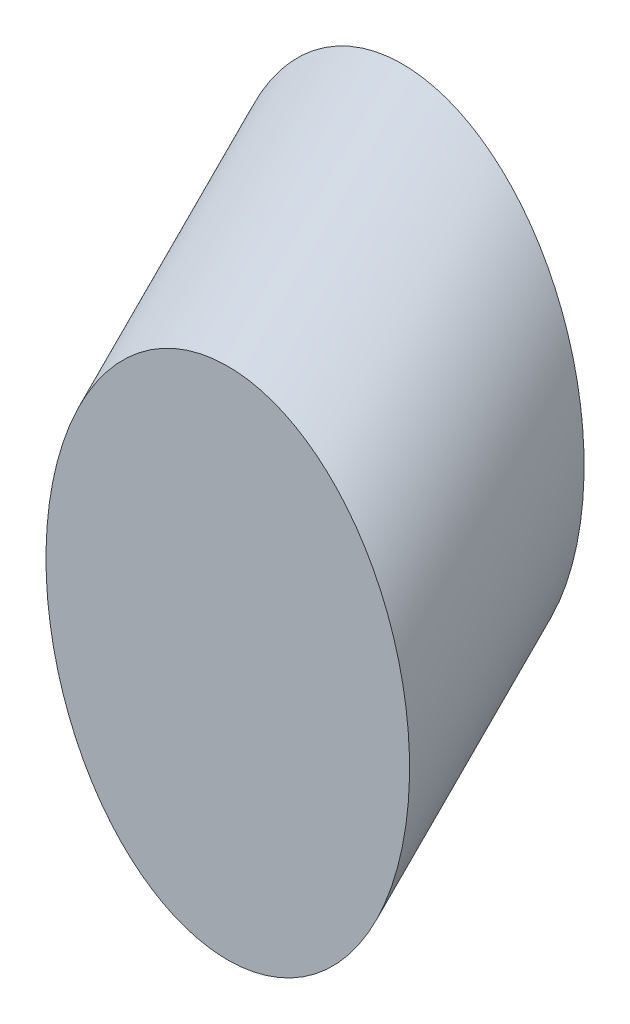
SolidWorks part; units mm, degrees
ref_plane "前视基准面" through (0, 0, 0) normal (0, 0, 1) x (1, 0, 0)
ref_plane "上视基准面" through (0, 0, 0) normal (0, 1, 0) x (1, 0, 0)
ref_plane "右视基准面" through (0, 0, 0) normal (1, 0, 0) x (0, 0, -1)
sketch "草图1" plane through (0, 0, 0) normal (0, 0, 1) x (1, 0, 0)
  ellipse E0 centre (54.3924, 35.7889) end of major axis (54.3924, 26.9489) minor radius 6.25
  dimension "D1" = 12.5
  dimension "D2" = 17.68
sketch3d "3D草图2"
  line L0 (55.1123, 27.0077, 0) -> (55.1123, 27.0077, -2.7888)
  line L3 (55.1123, 27.0077, 0) -> (55.1123, 22.573, 4.4347)
  line L4 (55.1123, 27.0077, 0) -> (55.1123, 28.9476, 0)
  spline S2 degree 3 poles (54.3924, 26.9489, 0) (66.8924, 26.9489, 0) (66.8924, 44.6289, 0) (54.3924, 44.6289, 0) (41.8924, 44.6289, 0) (41.8924, 26.9489, 0) (54.3924, 26.9489, 0) (66.8924, 26.9489, 0) (66.8924, 44.6289, 0) knots -0.5 0 0 0 0.5 0.5 0.5 1 1 1 1.5 1.5 1.5 weights 1 0.333333 0.333333 1 0.333333 0.333333 1 0.333333 0.333333 only from (54.3924, 26.9489, 0) to (54.3924, 26.9489, 0) construction
  dimension "D1" = 45
extrude "凸台-拉伸2" add sketch "草图1" along direction (0, -0.7071, 0.7071) on the side against the normal blind 8.4853
